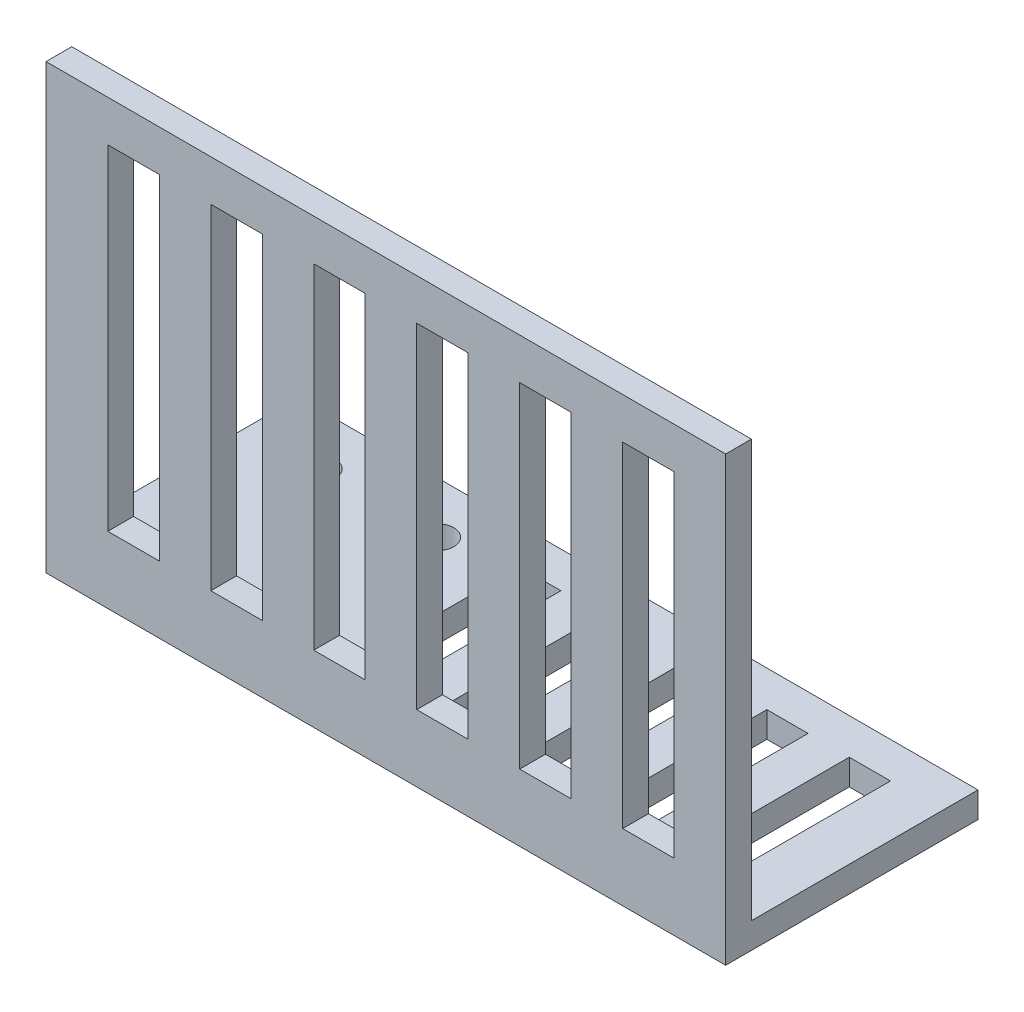
SolidWorks part; units mm, degrees
ref_plane "Front Plane" through (0, 0, 0) normal (0, 0, 1) x (1, 0, 0)
ref_plane "Top Plane" through (0, 0, 0) normal (0, 1, 0) x (1, 0, 0)
ref_plane "Right Plane" through (0, 0, 0) normal (1, 0, 0) x (0, 0, -1)
sketch "Sketch1" plane through (0, 0, 0) normal (0, 1, 0) x (1, 0, 0)
  line L0 (-33, 6) -> (-33, 16)
  line L1 (-33, 16) -> (33, 16)
  line L2 (33, 16) -> (33, 6)
  line L3 (33, 6) -> (33, -6)
  line L4 (33, -6) -> (-33, -6)
  line L5 (-33, -6) -> (-33, 6)
  circle A0 centre (-26, 11) radius 1.6
  circle A1 centre (-14.5, 11) radius 1.6
  point P7 (0, 16)
  point P9 (-33, 0)
  dimension "D3" = 3.2
  dimension "D5" = 5
  dimension "D6" = 7
  dimension "D7" = 11.5
  dimension "D1" = 12
  dimension "D2" = 66
  dimension "D4" = 5
extrude "Boss-Extrude1" add sketch "Sketch1" along normal blind 2.5
sketch "Sketch2" plane through (0, 0, 0) normal (0, 1, 0) x (1, 0, 0)
  line L0 (-33, -6) -> (-33, -8.5)
  line L1 (-33, -8.5) -> (33, -8.5)
  line L2 (33, -8.5) -> (33, -6)
  line L3 (33, -6) -> (-33, -6)
  line L4 (33, -6) -> (33, 16) construction
  dimension "D1" = 2.5
extrude "Boss-Extrude2" add sketch "Sketch2" along normal blind 43
sketch "Sketch3" plane through (0, 0, 0) normal (0, 0, 1) x (1, 0, 0)
  line L0 (28, 39) -> (28, 6.5)
  line L1 (28, 6.5) -> (23, 6.5)
  line L2 (23, 6.5) -> (23, 39)
  line L3 (23, 39) -> (28, 39)
  line L4 (33, 43) -> (-33, 43) construction
  line L5 (-33, 2.5) -> (33, 2.5) construction
  line L6 (33, 43) -> (33, 2.5) construction
  dimension "D1" = 5
  dimension "D2" = 4
  dimension "D3" = 4
  dimension "D4" = 5
extrude "Cut-Extrude1" cut sketch "Sketch3" along normal through all
pattern_linear "LPattern1" count 6 spacing 10 along (-1, 0, 0) of "Cut-Extrude1"
sketch "Sketch4" plane through (0, 0, 0) normal (0, 1, 0) x (1, 0, 0)
  line L0 (28, 12.5) -> (28, -2.5)
  line L1 (28, -2.5) -> (24, -2.5)
  line L2 (24, -2.5) -> (24, 12.5)
  line L3 (24, 12.5) -> (28, 12.5)
  line L4 (33, -6) -> (33, 16) construction
  line L5 (33, 16) -> (-33, 16) construction
  line L6 (-33, -6) -> (33, -6) construction
  dimension "D1" = 4
  dimension "D2" = 5
  dimension "D3" = 3.5
  dimension "D4" = 3.5
extrude "Cut-Extrude2" cut sketch "Sketch4" along normal through all
pattern_linear "LPattern2" count 5 spacing 8 along (-1, 0, 0) of "Cut-Extrude2"
